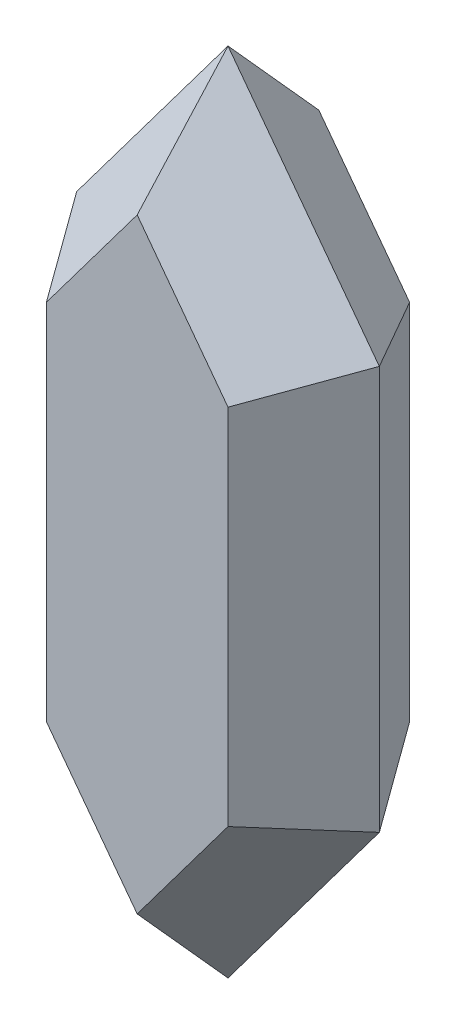
SolidWorks part; units mm, degrees
ref_plane "Alzado" through (0, 0, 0) normal (0, 0, 1) x (1, 0, 0)
ref_plane "Planta" through (0, 0, 0) normal (0, 1, 0) x (1, 0, 0)
ref_plane "Vista lateral" through (0, 0, 0) normal (1, 0, 0) x (0, 0, -1)
sketch "Base" plane through (0, 0, 0) normal (0, 0, 1) x (1, 0, 0)
  line L0 (12.5, 30) -> (12.5, 60) construction
  line L4 (27.5, 0) -> (27.5, 40)
  line L5 (12.5, 60) -> (12.5, -20) construction
  line L7 (12.5, 60) -> (27.5, 40)
  line L9 (12.5, -20) -> (27.5, 0)
  line L10 (12.5, -20) -> (-2.5, 0)
  line L11 (-2.5, 0) -> (-2.5, 40)
  line L12 (12.5, 60) -> (-2.5, 40)
  dimension "D1" = 40
  dimension "D2" = 20
  dimension "D3" = 15
  dimension "D4" = 20
ref_plane "Plano1" through (0, 0, 9) normal (0, 0, 1) x (1, 0, 0)
ref_plane "Plano2" through (0, 0, -9) normal (0, 0, -1) x (-1, 0, 0)
sketch "Base'" plane through (0, 0, 0) normal (0, 0, 1) x (1, 0, 0)
  line L0 (12.5, 30) -> (12.5, 60) construction
  line L4 (27.5, 0) -> (27.5, 40)
  line L5 (12.5, 60) -> (12.5, -20) construction
  line L7 (12.5, 60) -> (27.5, 40)
  line L9 (12.5, -20) -> (27.5, 0)
  line L10 (12.5, -20) -> (-2.5, 0)
  line L11 (-2.5, 0) -> (-2.5, 40)
  line L12 (12.5, 60) -> (-2.5, 40)
  dimension "D1" = 40
  dimension "D2" = 20
  dimension "D3" = 15
  dimension "D4" = 20
sketch "Extrude" plane through (0, 0, 9) normal (0, 0, 1) x (1, 0, 0)
  line L0 (-2.5, 40) -> (-2.5, 0) construction
  line L1 (-2.5, 0) -> (12.5, -20) construction
  line L2 (12.5, -20) -> (27.5, 0) construction
  line L3 (27.5, 0) -> (27.5, 40) construction
  line L4 (27.5, 40) -> (12.5, 60) construction
  line L5 (12.5, 60) -> (-2.5, 40) construction
  line L6 (3.5, 38) -> (3.5, 2)
  line L7 (3.5, 2) -> (12.5, -10)
  line L8 (12.5, -10) -> (21.5, 2)
  line L9 (21.5, 2) -> (21.5, 38)
  line L10 (21.5, 38) -> (12.5, 50)
  line L11 (12.5, 50) -> (3.5, 38)
  dimension "D1" = 6
loft "Recubrir3" add profiles "Base", "Extrude"
sketch "Croquis7" plane through (0, 0, -9) normal (0, 0, -1) x (-1, 0, 0)
  line L0 (-27.5, 40) -> (-12.5, 60) construction
  line L1 (-12.5, 60) -> (2.5, 40) construction
  line L2 (2.5, 40) -> (2.5, 0) construction
  line L3 (2.5, 0) -> (-12.5, -20) construction
  line L4 (-12.5, -20) -> (-27.5, 0) construction
  line L5 (-27.5, 0) -> (-27.5, 40) construction
  line L6 (-21.5, 38) -> (-12.5, 50)
  line L7 (-12.5, 50) -> (-3.5, 38)
  line L8 (-3.5, 38) -> (-3.5, 2)
  line L9 (-3.5, 2) -> (-12.5, -10)
  line L10 (-12.5, -10) -> (-21.5, 2)
  line L11 (-21.5, 2) -> (-21.5, 38)
  dimension "D1" = 6
loft "Recubrir4" add profiles "Base'", "Croquis7"
